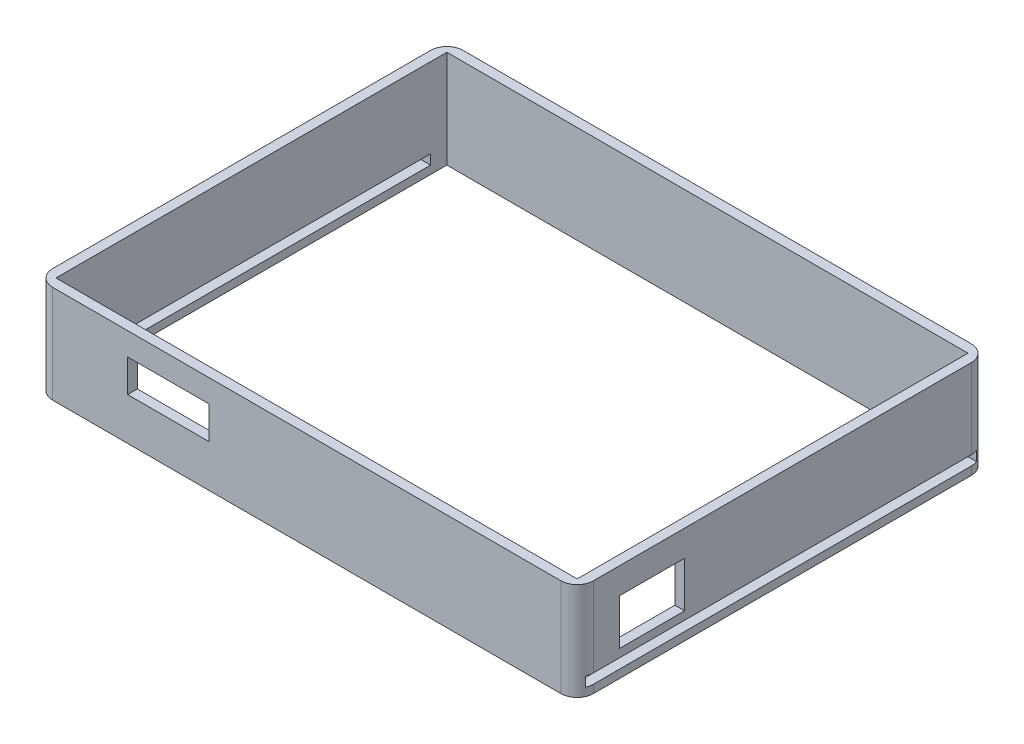
SolidWorks part; units mm, degrees
ref_plane "前视基准面" through (0, 0, 0) normal (0, 0, 1) x (1, 0, 0)
ref_plane "上视基准面" through (0, 0, 0) normal (0, 1, 0) x (1, 0, 0)
ref_plane "右视基准面" through (0, 0, 0) normal (1, 0, 0) x (0, 0, -1)
sketch "草图1" plane through (0, 0, 0) normal (0, 1, 0) x (1, 0, 0)
  line L1 (-80, 60) -> (80, 60)
  line L2 (-80, 60) -> (-80, -60)
  line L3 (-80, -60) -> (80, -60)
  line L4 (80, 60) -> (80, -60)
  line L5 (-80, 60) -> (80, -60) construction
  line L6 (-80, -60) -> (80, 60) construction
  line L7 (-83, 63) -> (83, 63)
  line L8 (-83, 63) -> (-83, -63)
  line L9 (-83, -63) -> (83, -63)
  line L10 (83, 63) -> (83, -63)
  line L11 (-83, 63) -> (83, -63) construction
  line L12 (-83, -63) -> (83, 63) construction
  point P0 (0, 0)
  point P6 (0, 0)
  dimension "D1" = 160
  dimension "D2" = 120
  dimension "D3" = 166
  dimension "D4" = 126
extrude "凸台-拉伸1" add sketch "草图1" along normal blind 30
fillet "圆角1" radius 5 4 edges at (-83, 15, -63) (-83, 15, 63) (83, 15, -63) (83, 15, 63)
sketch "草图2" plane through (0, 0, 0) normal (0, 0, 1) x (1, 0, 0)
  line L0 (0, 50.1861) -> (0, -27.5035) construction
  line L1 (0, 23) -> (-70.0429, 23) construction
  line L2 (-78, 30) -> (78, 30) construction
  line L4 (-55, 23) -> (-30, 23)
  line L5 (-55, 23) -> (-55, 13)
  line L6 (-55, 13) -> (-30, 13)
  line L7 (-30, 23) -> (-30, 13)
  point P6 (0, 30)
  dimension "D1" = 7
  dimension "D2" = 30
  dimension "D3" = 25
  dimension "D4" = 10
extrude "切除-拉伸1" cut sketch "草图2" along normal blind 100
sketch "草图3" plane through (0, 0, 0) normal (1, 0, 0) x (0, 0, -1)
  line L0 (0, 39.2752) -> (0, -9.2752) construction
  line L1 (0, 15) -> (-80, 15) construction
  line L2 (-58, 30) -> (58, 30) construction
  line L3 (-50, 22) -> (-30, 22)
  line L4 (-50, 22) -> (-50, 8)
  line L5 (-50, 8) -> (-30, 8)
  line L6 (-30, 22) -> (-30, 8)
  line L7 (-50, 22) -> (-30, 8) construction
  line L8 (-50, 8) -> (-30, 22) construction
  point P5 (-40, 15)
  dimension "D1" = 20
  dimension "D2" = 14
  dimension "D3" = 15
  dimension "D4" = 30
extrude "切除-拉伸2" cut sketch "草图3" along normal blind 100
sketch "草图4" plane through (0, 0, 0) normal (1, 0, 0) x (0, 0, -1)
  line L0 (0, -7.7668) -> (0, 34.3778) construction
  line L1 (0, 0) -> (0, 4) construction
  line L2 (-58, 0) -> (58, 0) construction
  line L3 (0, 4) -> (26.7437, 4) construction
  line L5 (-60, 5.5) -> (60, 5.5)
  line L6 (-60, 5.5) -> (-60, 2.5)
  line L7 (-60, 2.5) -> (60, 2.5)
  line L8 (60, 5.5) -> (60, 2.5)
  line L9 (-60, 5.5) -> (60, 2.5) construction
  line L10 (-60, 2.5) -> (60, 5.5) construction
  dimension "D1" = 4
  dimension "D2" = 120
  dimension "D3" = 3
extrude "切除-拉伸3" cut sketch "草图4" along normal blind 100
sketch "草图5" plane through (0, 0, 0) normal (1, 0, 0) x (0, 0, -1)
  line L0 (0, 32.9228) -> (0, -9.6893) construction
  line L1 (0, 0) -> (0, 4) construction
  line L2 (0, 4) -> (22.4585, 4) construction
  line L3 (-58, 0) -> (58, 0) construction
  line L5 (-55, 5.5) -> (55, 5.5)
  line L6 (-55, 5.5) -> (-55, 2.5)
  line L7 (-55, 2.5) -> (55, 2.5)
  line L8 (55, 5.5) -> (55, 2.5)
  line L9 (-55, 5.5) -> (55, 2.5) construction
  line L10 (-55, 2.5) -> (55, 5.5) construction
  dimension "D1" = 4
  dimension "D2" = 110
  dimension "D3" = 3
extrude "切除-拉伸4" cut sketch "草图5" against normal blind 100
